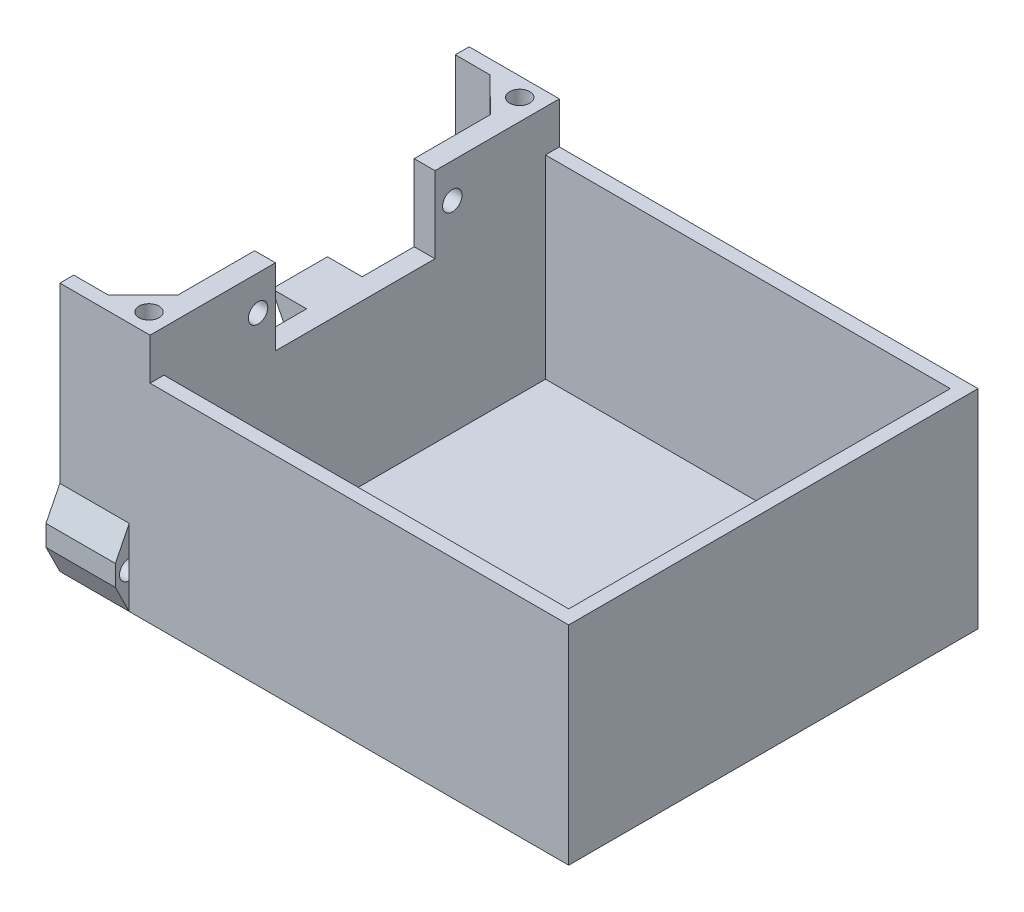
SolidWorks part; units mm, degrees
ref_plane "Front Plane" through (0, 0, 0) normal (0, 0, 1) x (1, 0, 0)
ref_plane "Top Plane" through (0, 0, 0) normal (0, 1, 0) x (1, 0, 0)
ref_plane "Right Plane" through (0, 0, 0) normal (1, 0, 0) x (0, 0, -1)
sketch "Sketch1" plane through (0, 0, 0) normal (0, 1, 0) x (1, 0, 0)
  line L1 (0, 0) -> (70, 0)
  line L2 (0, 0) -> (0, -55)
  line L3 (0, -55) -> (70, -55)
  line L4 (70, 0) -> (70, -55)
  dimension "D1" = 55
  dimension "D2" = 70
extrude "Boss-Extrude1" add sketch "Sketch1" along normal blind 2
sketch "Sketch2" plane through (0, 0, 0) normal (0, 1, 0) x (1, 0, 0)
  line L0 (70, 0) -> (0, 0) construction
  line L1 (-1.3503, 2) -> (72, 2)
  line L2 (-1.3503, 2) -> (-1.3503, -57)
  line L3 (-1.3503, -57) -> (72, -57)
  line L4 (72, 2) -> (72, -57)
  line L5 (0, -55) -> (70, -55) construction
  line L6 (0, 0) -> (0, -55) construction
  line L7 (70, -55) -> (70, 0) construction
  dimension "D1" = 2
  dimension "D2" = 2
  dimension "D3" = 1.3503
  dimension "D4" = 2
extrude "Boss-Extrude3" add sketch "Sketch2" along normal blind 2
sketch "Sketch3" plane through (0, 2, 0) normal (0, 1, 0) x (1, 0, 0)
  line L0 (-1.3503, 2) -> (72, 2)
  line L1 (72, 2) -> (72, -57)
  line L2 (72, -57) -> (-1.3503, -57)
  line L3 (-1.3503, -57) -> (-1.3503, -55)
  line L4 (-1.3503, 2) -> (-1.3503, -57) construction
  line L5 (-1.3503, -55) -> (70, -55)
  line L6 (70, -55) -> (70, 0)
  line L7 (70, 0) -> (-1.3503, 0)
  line L8 (-1.3503, 0) -> (-1.3503, 2)
  dimension "D1" = 2
  dimension "D2" = 2
extrude "Boss-Extrude4" add sketch "Sketch3" along normal blind 28
sketch "Sketch5" plane through (0, 2, 0) normal (0, 1, 0) x (1, 0, 0)
  line L0 (-1.3503, 0) -> (70, 0) construction
  line L1 (8.6497, 0) -> (11.6497, 0)
  line L2 (8.6497, 0) -> (8.6497, -55)
  line L3 (8.6497, -55) -> (11.6497, -55)
  line L4 (11.6497, 0) -> (11.6497, -55)
  line L5 (70, -55) -> (-1.3503, -55) construction
  line L6 (-1.3503, 0) -> (-1.3503, -55) construction
  line L7 (3.6497, 0) -> (8.6497, -4.9272)
  line L8 (8.6497, -4.9272) -> (8.6497, 0)
  line L9 (3.6497, 0) -> (8.6497, 0)
  line L10 (3.6497, -55) -> (8.6497, -49.9262)
  line L11 (8.6497, -49.9262) -> (8.6497, -55)
  line L12 (3.6497, -55) -> (8.6497, -55)
  line L13 (-1.3503, 0) -> (8.6497, 0) construction
  line L14 (-1.3503, -55) -> (8.6497, -55) construction
  line M8 (-1.3503, -55) -> (70, -55)
  line M10 (70, 0) -> (-1.3503, 0)
  dimension "D1" = 3
  dimension "D2" = 10
  dimension "D3" = 4.9272
extrude "Boss-Extrude5" add sketch "Sketch5" along normal blind 34 contours L4 L2 M10 M8 | L7 L2 M10 | L10 L2 M8
sketch "Sketch7" plane through (0, 36, 0) normal (0, 1, 0) x (1, 0, 0)
  line L0 (8.6497, -4.9272) -> (8.6497, -49.9262) construction
  line L1 (8.6497, -15.9267) -> (11.6497, -15.9267)
  line L2 (8.6497, -15.9267) -> (8.6497, -38.9267)
  line L3 (8.6497, -38.9267) -> (11.6497, -38.9267)
  line L4 (11.6497, -15.9267) -> (11.6497, -38.9267)
  line L5 (11.6497, 0) -> (11.6497, -55) construction
  point P8 (8.6497, -27.4267)
  point P9 (8.6497, -27.4267)
  dimension "D1" = 23
extrude "Cut-Extrude1" cut sketch "Sketch7" against normal blind 11
sketch "Sketch9" plane through (8.6497, 0, 0) normal (-1, 0, 0) x (0, 0, 1)
  line L0 (15.9267, 25) -> (15.9267, 36) construction
  line L1 (38.9267, 25) -> (38.9267, 36) construction
  line L2 (38.9267, 36) -> (49.9262, 36) construction
  circle A0 centre (13.4267, 31) radius 1.4
  circle A1 centre (41.4267, 31) radius 1.4
  dimension "D2" = 2.8
  dimension "D4" = 2.8
  dimension "D1" = 2.5
  dimension "D3" = 2.5
  dimension "D5" = 5
  dimension "D6" = 5
extrude "Cut-Extrude2" cut sketch "Sketch9" against normal blind 11
sketch "Sketch10" plane through (8.6497, 0, 0) normal (-1, 0, 0) x (0, 0, 1)
  line L0 (15.9267, 25) -> (38.9267, 25) construction
  line L1 (31.4267, 25) -> (23.4267, 25)
  line L2 (31.4267, 25) -> (31.4267, 15)
  line L3 (31.4267, 15) -> (23.4267, 15)
  line L4 (23.4267, 25) -> (23.4267, 15)
  line L5 (15.9267, 25) -> (38.9267, 25) construction
  point P6 (27.4267, 25)
  point P7 (27.4267, 25)
  dimension "D1" = 10
  dimension "D2" = 8
extrude "Boss-Extrude6" add sketch "Sketch10" along normal blind 5
sketch "Sketch11" plane through (0, 0, 23.4267) normal (0, 0, -1) x (-1, 0, 0)
  line L0 (-8.6497, 15) -> (-3.6497, 25)
  line L1 (-3.6497, 25) -> (-3.6497, 15)
  line L2 (-3.6497, 15) -> (-8.6497, 15)
extrude "Cut-Extrude3" cut sketch "Sketch11" against normal up to next
sketch "Sketch12" plane through (0, 30, 0) normal (0, 1, 0) x (1, 0, 0)
  line L1 (-1.3503, 2) -> (11.6497, 2)
  line L2 (-1.3503, 2) -> (-1.3503, 0)
  line L3 (-1.3503, 0) -> (11.6497, 0)
  line L4 (11.6497, 2) -> (11.6497, 0)
  line L5 (-1.3503, -57) -> (11.6497, -57)
  line L6 (-1.3503, -57) -> (-1.3503, -55)
  line L7 (-1.3503, -55) -> (11.6497, -55)
  line L8 (11.6497, -57) -> (11.6497, -55)
extrude "Boss-Extrude7" add sketch "Sketch12" along normal blind 6
sketch "Sketch13" plane through (0, 36, 0) normal (0, 1, 0) x (1, 0, 0)
  line L0 (3.6497, 0) -> (8.6497, -4.9272) construction
  line L1 (3.6497, -55) -> (8.6497, -49.9262) construction
  circle A0 centre (8.6111, -0.6772) radius 1.45
  circle A1 centre (8.6735, -54.1762) radius 1.45
  dimension "D1" = 2.9
  dimension "D2" = 2.9
  dimension "D3" = 3
  dimension "D4" = 4.25
  dimension "D5" = 3
  dimension "D6" = 4.25
extrude "Cut-Extrude4" cut sketch "Sketch13" against normal blind 10
sketch "Sketch14" plane through (-1.3503, 0, 0) normal (-1, 0, 0) x (0, 0, 1)
  line L0 (-2, 0) -> (-4, 4)
  line L1 (-4, 4) -> (-4, 7)
  line L2 (-4, 7) -> (-2, 11)
  line L3 (-2, 36) -> (-2, 0) construction
  line L4 (-2, 11) -> (-2, 0)
  line L5 (57, 0) -> (57, 11)
  line L6 (57, 36) -> (57, 0) construction
  line L7 (57, 11) -> (59, 7)
  line L8 (59, 7) -> (59, 4)
  line L9 (59, 4) -> (57, 0)
  dimension "D1" = 4
  dimension "D2" = 4
  dimension "D3" = 3
  dimension "D4" = 2
  dimension "D5" = 2
  dimension "D6" = 4
  dimension "D7" = 3
  dimension "D8" = 4
extrude "Boss-Extrude8" add sketch "Sketch14" against normal blind 10
sketch "Sketch15" plane through (-1.3503, 0, 0) normal (-1, 0, 0) x (0, 0, 1)
  circle A0 centre (-2, 5.25) radius 1.4
  circle A1 centre (57, 5.25) radius 1.4
  dimension "D1" = 2.8
  dimension "D2" = 2.8
  dimension "D3" = 3.25
  dimension "D4" = 3.25
  dimension "D5" = 2
  dimension "D6" = 2
extrude "Cut-Extrude5" cut sketch "Sketch15" against normal blind 10
